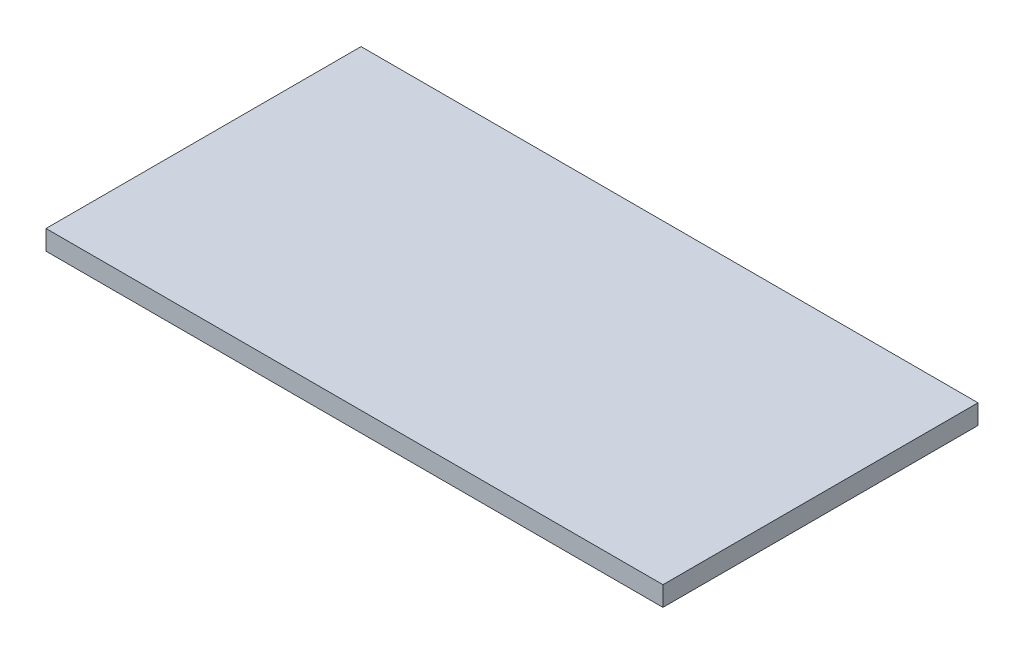
SolidWorks part; units mm, degrees
ref_plane "Front Plane" through (0, 0, 0) normal (0, 0, 1) x (1, 0, 0)
ref_plane "Top Plane" through (0, 0, 0) normal (0, 1, 0) x (1, 0, 0)
ref_plane "Right Plane" through (0, 0, 0) normal (1, 0, 0) x (0, 0, -1)
sketch "Sketch1" plane through (0, 0, 0) normal (0, 1, 0) x (1, 0, 0)
  line L1 (282, -144) -> (-282, -144)
  line L2 (282, -144) -> (282, 144)
  line L3 (282, 144) -> (-282, 144)
  line L4 (-282, -144) -> (-282, 144)
  line L5 (282, -144) -> (-282, 144) construction
  line L6 (282, 144) -> (-282, -144) construction
  point P0 (0, 0)
  dimension "D1" = 288
  dimension "D2" = 564
extrude "Boss-Extrude1" add sketch "Sketch1" along normal blind 18
sketch "Sketch2" plane through (0, 18, 0) normal (0, 1, 0) x (1, 0, 0)
  line L0 (282, 144) -> (-282, 144) construction
  line L2 (80, -145.6809) -> (-80, -145.6809)
  line L3 (79.7759, 59.9832) -> (79.7759, 265.6809)
  line L4 (79.7759, 265.6809) -> (-80, 265.6809)
  line L5 (-80, 54) -> (-80, 265.6809)
  line L6 (28.2818, -20.8341) -> (-80, 265.6809) construction
  line L7 (79.7759, 265.6809) -> (-28.2125, -20.8602) construction
  arc A0 (-80, 54) -> (79.7759, 59.9832) centre (0, 54) ccw
  line M4 (282, 144) -> (-282, 144)
  dimension "D1" = 80
  dimension "D2" = 90
extrude "Cut-Extrude1" [suppressed] cut sketch "Sketch2" against normal through all contours L5 A0 L3 M4
equation "\"H_DSP\"=18"
equation "\"D1@Boss-Extrude1\"=\"H_DSP\""
